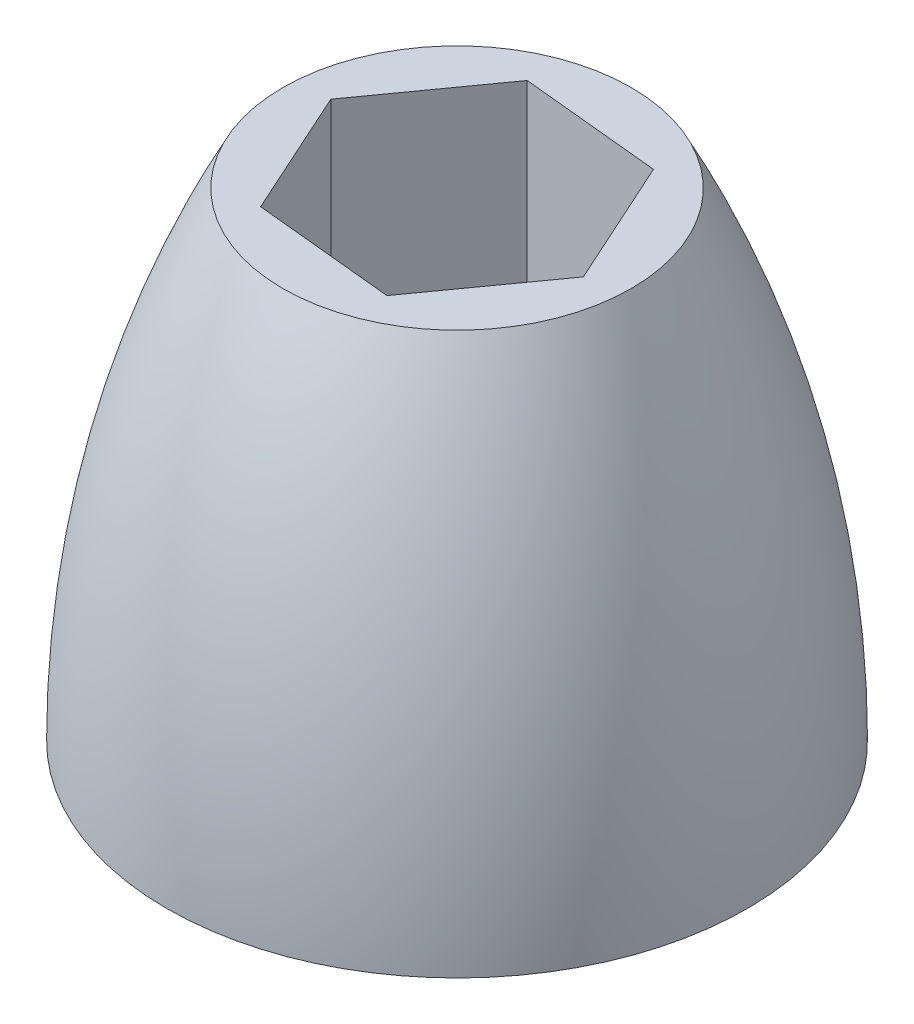
SolidWorks part; units mm, degrees
ref_plane "Front Plane" through (0, 0, 0) normal (0, 0, 1) x (1, 0, 0)
ref_plane "Top Plane" through (0, 0, 0) normal (0, 1, 0) x (1, 0, 0)
ref_plane "Right Plane" through (0, 0, 0) normal (1, 0, 0) x (0, 0, -1)
sketch "Sketch1" plane through (0, 0, 0) normal (0, 1, 0) x (1, 0, 0)
  circle A0 centre (0, 0) radius 19.05
extrude "Boss-Extrude1" add sketch "Sketch1" along normal blind 104.775
sketch "Sketch2" plane through (0, 0, 0) normal (0, -1, 0) x (1, 0, 0)
  line L1 (-15.3236, -1.5108) -> (-6.3534, -14.026)
  line L2 (-6.3534, -14.026) -> (8.9702, -12.5153)
  line L3 (8.9702, -12.5153) -> (15.3236, 1.5108)
  line L4 (15.3236, 1.5108) -> (6.3534, 14.026)
  line L5 (6.3534, 14.026) -> (-8.9702, 12.5153)
  line L6 (-8.9702, 12.5153) -> (-15.3236, -1.5108)
  circle A0 centre (0, 0) radius 13.335 construction
extrude "Cut-Extrude1" cut sketch "Sketch2" against normal up to surface (104.775 mm away) up to face at (0, 104.775, 19.05)
sketch "Sketch4" plane through (0, 0, 0) normal (0, 0, 1) x (1, 0, 0)
  line L0 (-19.05, 104.775) -> (-19.05, 0)
  line L1 (0, 0) -> (0, 104.775) construction
  line L2 (19.05, 104.775) -> (-19.05, 104.775) construction
  arc A0 (-19.05, 0) -> (-19.05, 104.775) centre (82.6492, 52.3875) cw
  point P5 (-31.75, 52.3875)
  point P6 (-19.05, 52.3875)
  dimension "D1" = 12.7
revolve "Revolve1" add sketch "Sketch4" angle 360 about L1
sketch "Sketch5" plane through (0, 0, 0) normal (0, 0, 1) x (1, 0, 0)
  line L1 (-39.6693, 52.3875) -> (39.39, 52.3875)
  line L2 (-39.6693, 52.3875) -> (-39.6693, 0)
  line L3 (-39.6693, 0) -> (39.39, 0)
  line L4 (39.39, 52.3875) -> (39.39, 0)
extrude "Cut-Extrude2" cut sketch "Sketch5" against normal through all both and the other way through all
